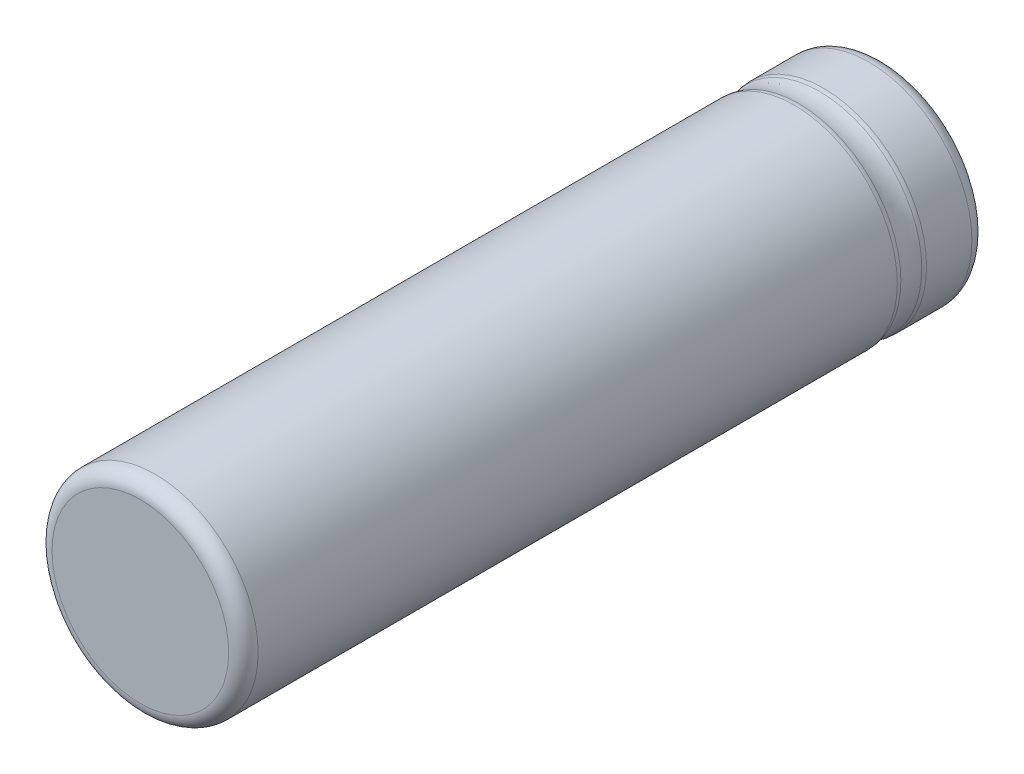
SolidWorks part; units mm, degrees
ref_plane "Front Plane" through (0, 0, 0) normal (0, 0, 1) x (1, 0, 0)
ref_plane "Top Plane" through (0, 0, 0) normal (0, 1, 0) x (1, 0, 0)
ref_plane "Right Plane" through (0, 0, 0) normal (1, 0, 0) x (0, 0, -1)
sketch "Sketch1" plane through (0, 0, 0) normal (0, 0, 1) x (1, 0, 0)
  circle A0 centre (0, 0) radius 7
  dimension "D1" = 14
extrude "Extrude1" add sketch "Sketch1" along normal blind 50.5
sketch "Sketch2" plane through (0, 0, 0) normal (1, 0, 0) x (0, 0, -1)
  line L0 (0, 0) -> (-22.6754, 0) construction
  circle A0 centre (-5.0771, 9.3558) radius 2.5
  dimension "D1" = 5
revolve "Cut-Revolve1" cut sketch "Sketch2" angle 360 about L0
fillet "Fillet1" radius 1 4 edges at (7, 0, 0) (7, 0, 50.5) (-7, 0, 5.9138) (7, 0, 4.2404)
